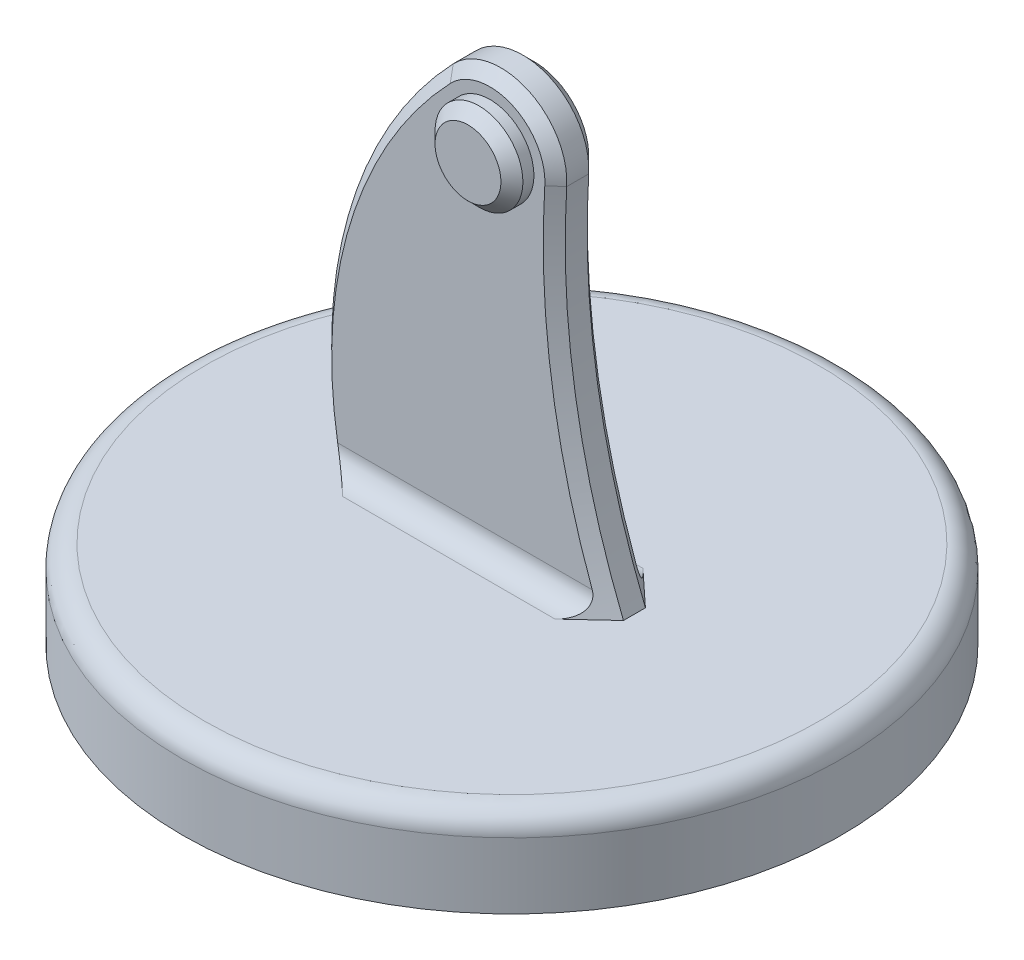
SolidWorks part; units mm, degrees
material "PE High Density"
ref_plane "Front Plane" through (0, 0, 0) normal (0, 0, 1) x (1, 0, 0)
ref_plane "Top Plane" through (0, 0, 0) normal (0, 1, 0) x (1, 0, 0)
ref_plane "Right Plane" through (0, 0, 0) normal (1, 0, 0) x (0, 0, -1)
sketch "Sketch1" plane through (0, 0, 0) normal (0, 1, 0) x (1, 0, 0)
  circle A0 centre (0, 0) radius 75
  dimension "D1" = 150
extrude "Boss-Extrude1" add sketch "Sketch1" along normal blind 20
fillet "Fillet1" radius 5 1 edges at (0, 20, 75)
sketch "Sketch2" plane through (0, 0, 0) normal (0, 0, 1) x (1, 0, 0)
  line L0 (0, 0) -> (0, 100) construction
  line L2 (-75, 15) -> (75, 15) construction
  line L3 (-35, 15) -> (30, 15)
  arc A0 (14.9706, 99.062) -> (-10.8492, 110.3583) centre (0, 100) ccw
  arc A1 (-35, 15) -> (-10.8492, 110.3583) centre (61.4788, 41.3028) cw
  arc A2 (30, 15) -> (14.9706, 99.062) centre (194.6184, 87.8065) cw
  dimension "D4" = 30
  dimension "D5" = 30
  dimension "D6" = 180
  dimension "D2" = 100
  dimension "D1" = 35
  dimension "D3" = 100
extrude "Boss-Extrude2" add sketch "Sketch2" along normal mid plane 10
chamfer "Chamfer1" distance 2.5 angle 45 6 edges at (16.9703, 58.8038, 5) (-34.7965, 68.3412, 5) (6.0123, 113.7423, 5) (-34.7965, 68.3412, -5) (6.0123, 113.7423, -5) (16.9703, 58.8038, -5)
fillet "Fillet2" radius 5 2 edges at (-4.2415, 20, 5) (-4.2415, 20, -5)
sketch "Sketch3" plane through (0, 0, 5) normal (0, 0, 1) x (1, 0, 0)
  circle A0 centre (0, 100) radius 10
  dimension "D1" = 20
extrude "Boss-Extrude3" add sketch "Sketch3" along normal blind 5
chamfer "Chamfer2" distance 2.5 angle 45 1 edges at (10, 100, 10)
sketch "Sketch4" plane through (0, 0, -5) normal (0, 0, -1) x (-1, 0, 0)
  circle A0 centre (0, 100) radius 5
  dimension "D1" = 10
extrude "Cut-Extrude1" cut sketch "Sketch4" against normal blind 10
